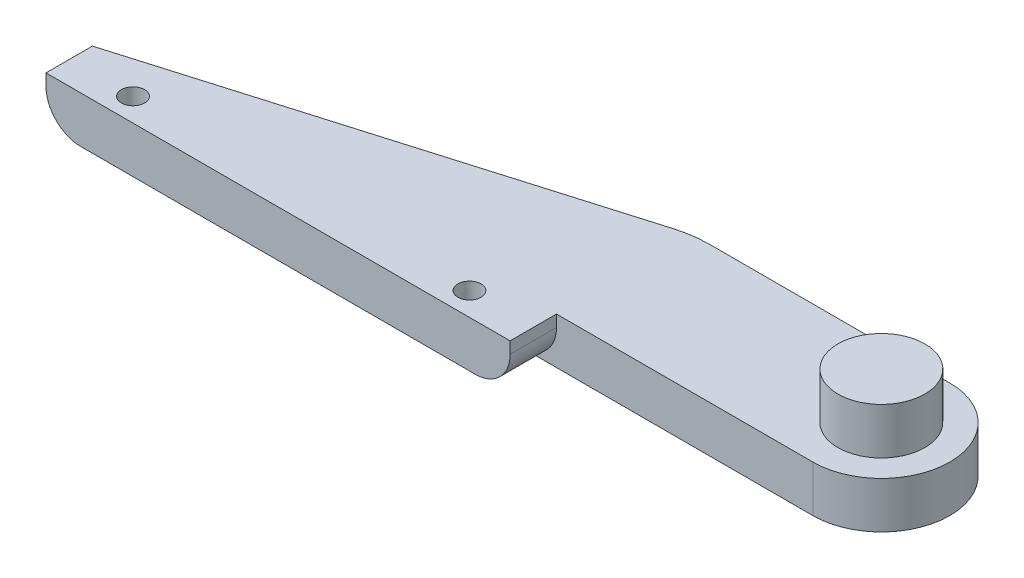
SolidWorks part; units mm, degrees
ref_plane "Front Plane" through (0, 0, 0) normal (0, 0, 1) x (1, 0, 0)
ref_plane "Top Plane" through (0, 0, 0) normal (0, 1, 0) x (1, 0, 0)
ref_plane "Right Plane" through (0, 0, 0) normal (1, 0, 0) x (0, 0, -1)
sketch "Sketch1" plane through (0, 0, 0) normal (0, 1, 0) x (1, 0, 0)
  line L0 (-20, 2) -> (20, 13.8)
  line L1 (-20, -2) -> (20, -2)
  line L2 (-20, -2) -> (-20, 2)
  line L3 (-20, 2) -> (20, 2) construction
  line L4 (20, -2) -> (20, 2)
  line L5 (-20, -2) -> (20, 2) construction
  line L6 (-20, 2) -> (20, -2) construction
  line L7 (20, 13.8) -> (20, 2) construction
  line L8 (20, 7.9) -> (48, 7.9) construction
  line L11 (20, 13.8) -> (42.1, 13.8)
  line L12 (42.1, 13.8) -> (42.1, 2) construction
  line L13 (20, 2) -> (42.1, 2)
  arc A2 (42.1, 13.8) -> (42.1, 2) centre (42.1, 7.9) cw
  point P0 (0, 0)
extrude "Boss-Extrude2" add sketch "Sketch1" along normal blind 4
ref_plane "Plane1" through (0, -4, 0) normal (0, -1, 0) x (-1, 0, 0)
sketch "Sketch2" plane through (0, 0, 0) normal (0, 1, 0) x (1, 0, 0)
  line L0 (42.1, 13.8) -> (42.1, 2) construction
  line L5 (26.1497, 7.9) -> (45.7842, 7.9) construction
  line L6 (42.1, 18.1892) -> (42.1, -2.3892) construction
  line L7 (27.9813, 9.8929) -> (39.8678, 10.8763) construction
  line L8 (27.9813, 5.9071) -> (39.8997, 4.9) construction
  circle A9 centre (42.1, 7.9) radius 3.6842 construction
  arc A16 (27.9813, 9.8929) -> (27.9813, 5.9071) centre (28.1497, 7.9) ccw construction
  arc A17 (39.8678, 10.8763) -> (39.8997, 4.9) centre (42.1, 7.9) ccw construction
  point P0 (53.3853, 10.5001)
  point P3 (46.1609, 22.3448)
  point P5 (49.6378, 19.3514)
  point P29 (51.9992, 11.3401)
  point P37 (42.1, 7.9)
ref_plane "Plane2" through (0, 0, 0) normal (0, -1, 0) x (-1, 0, 0)
sketch "Sketch4" plane through (0, 4, 0) normal (0, -1, 0) x (-1, 0, 0)
  line L4 (-42.1, 2) -> (-42.1, 13.8) construction
  circle A1 centre (-42.1, 7.9) radius 3.7462
extrude "Boss-Extrude3" add sketch "Sketch4" against normal blind 4
sketch "Sketch5" plane through (0, 0, 0) normal (0, -1, 0) x (-1, 0, 0)
  line L0 (20, 0) -> (14.5, 0) construction
  line L1 (20, 2) -> (20, -2) construction
  line L2 (-20, 0) -> (-14.5, 0) construction
  line L3 (-20, -2) -> (-20, 2) construction
  circle A0 centre (14.5, 0) radius 1
  circle A1 centre (-14.5, 0) radius 1
extrude "Cut-Extrude1" cut sketch "Sketch5" against normal through all
fillet "Fillet1" radius 10 1 edges at (20, 2, -13.8)
fillet "Fillet3" radius 3 2 edges at (-20, 0, 0) (20, 0, 0)
